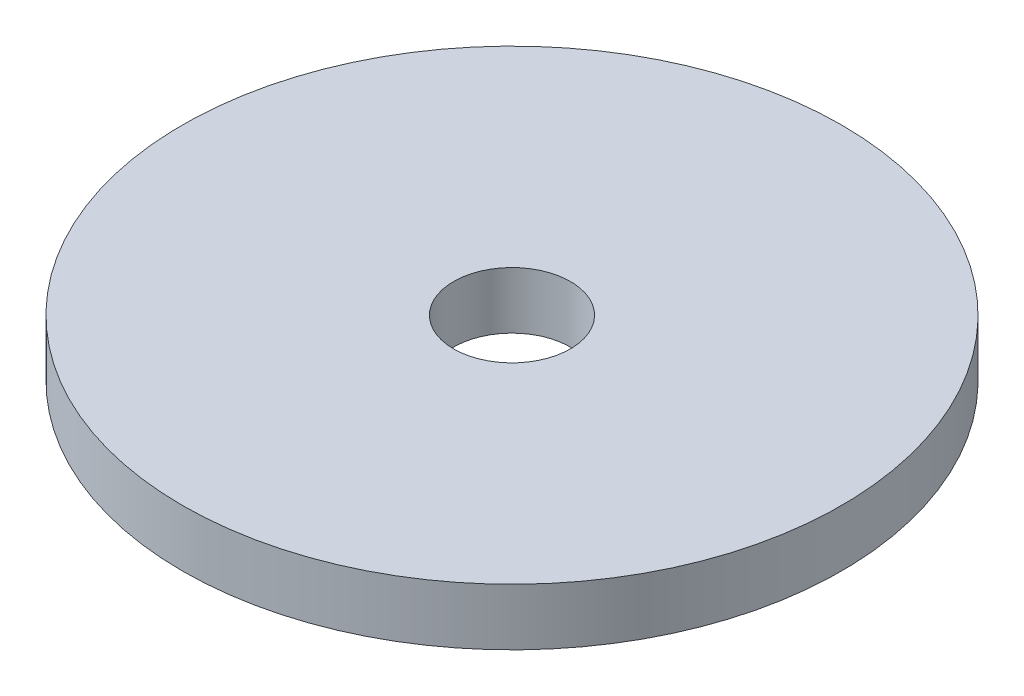
SolidWorks part; units mm, degrees
material "C-Glass Fiber"
ref_plane "Front Plane" through (0, 0, 0) normal (0, 0, 1) x (1, 0, 0)
ref_plane "Top Plane" through (0, 0, 0) normal (0, 1, 0) x (1, 0, 0)
ref_plane "Right Plane" through (0, 0, 0) normal (1, 0, 0) x (0, 0, -1)
sketch "Sketch1" plane through (0, 0, 0) normal (0, 1, 0) x (1, 0, 0)
  circle A0 centre (0, 0) radius 18.415
  dimension "D1" = 36.83
extrude "Boss-Extrude1" add sketch "Sketch1" along normal blind 3.175
sketch "Sketch2" plane through (0, 3.175, 0) normal (0, 1, 0) x (1, 0, 0)
  point P0 (0, 0)
hole_wizard "1/4 Clearance Hole1" positions "Sketch2" profile "Sketch3" hole size "1/4" standard "ANSI Inch"
sketch "Sketch3" plane through (0, 3.175, 0) normal (1, 0, 0) x (0, 0, 1)
  line L0 (0, 0) -> (0, 27.3611)
  line L1 (0, 27.3611) -> (3.2639, 25.4)
  line L2 (3.2639, 25.4) -> (3.2639, 0)
  line L5 (3.2639, 0) -> (0, 0)
  line L10 (0, 27.3611) -> (-3.2639, 25.4) construction
  line L11 (0, -6.35) -> (0, 107.95) construction
  dimension "Hole Dia." = 6.5278
  dimension "Hole Depth" = 25.4
  dimension "Drill Angle" = 118
